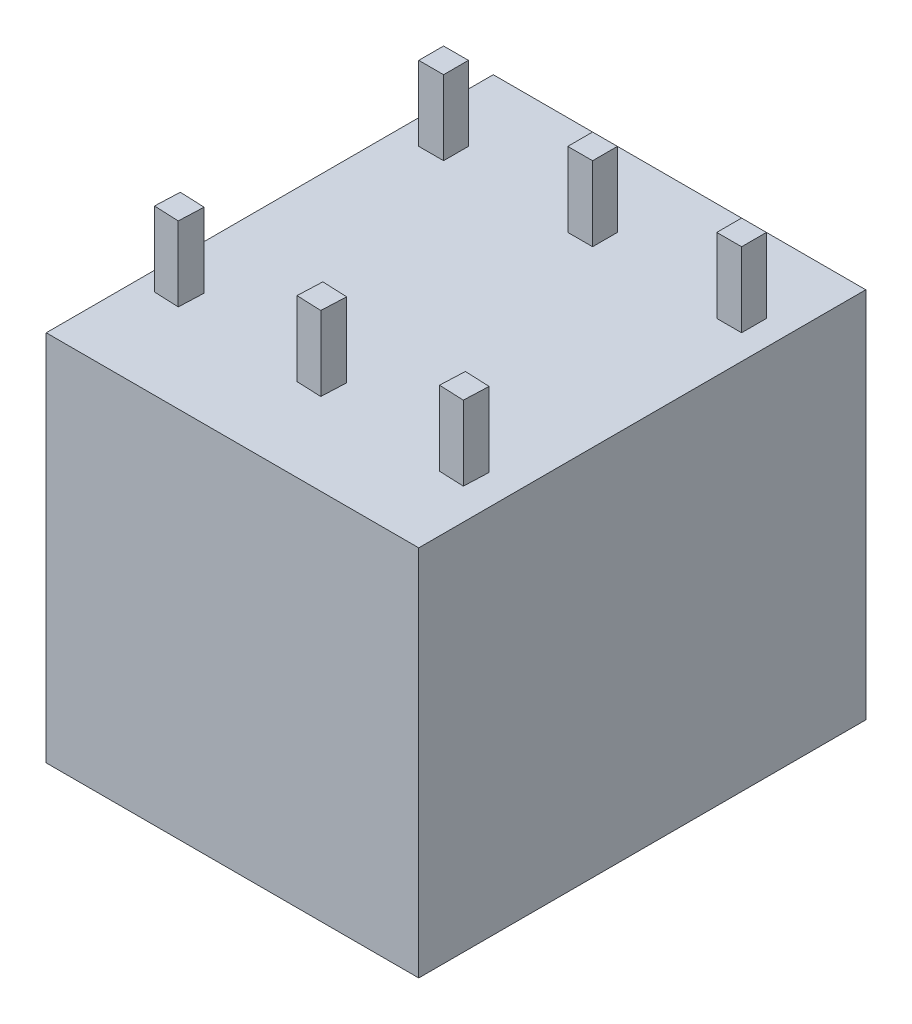
SolidWorks part; units mm, degrees
ref_plane "Plan de face" through (0, 0, 0) normal (0, 0, 1) x (1, 0, 0)
ref_plane "Plan de dessus" through (0, 0, 0) normal (0, 1, 0) x (1, 0, 0)
ref_plane "Plan de droite" through (0, 0, 0) normal (1, 0, 0) x (0, 0, -1)
sketch "Esquisse1" plane through (0, 0, 0) normal (0, 1, 0) x (1, 0, 0)
  line L1 (0, 0) -> (15, 0)
  line L2 (0, 0) -> (0, 18)
  line L3 (0, 18) -> (15, 18)
  line L4 (15, 0) -> (15, 18)
  dimension "D1" = 15
  dimension "D2" = 18
extrude "Boss.-Extru.1" add sketch "Esquisse1" along normal blind 15
sketch "Esquisse2" plane through (0, 15, 0) normal (0, 1, 0) x (1, 0, 0)
  line L0 (0, 18) -> (0, 0) construction
  line L1 (1, 15) -> (2, 15)
  line L2 (1, 15) -> (1, 14)
  line L3 (1, 14) -> (2, 14)
  line L4 (2, 15) -> (2, 14)
  line L5 (15, 18) -> (0, 18) construction
  line L6 (15, 18) -> (0, 18) construction
  line L7 (7, 15) -> (8, 15)
  line L8 (7, 15) -> (7, 14)
  line L9 (7, 14) -> (8, 14)
  line L10 (8, 15) -> (8, 14)
  line L11 (7.5, 18) -> (7.5, 0) construction
  line L12 (0, 0) -> (15, 0) construction
  line L13 (0, 9.3194) -> (15, 9) construction
  line L14 (15, 0) -> (15, 18) construction
  line L15 (14, 14) -> (13, 14)
  line L16 (14, 15) -> (14, 14)
  line L17 (14, 15) -> (13, 15)
  line L18 (13, 15) -> (13, 14)
  line L19 (12.7464, 3.0906) -> (12.789, 4.0897)
  line L20 (13.7455, 3.048) -> (12.7464, 3.0906)
  line L21 (13.7455, 3.048) -> (13.7881, 4.0471)
  line L22 (13.7881, 4.0471) -> (12.789, 4.0897)
  line L23 (7.7509, 3.3034) -> (7.7935, 4.3025)
  line L24 (6.7944, 4.3451) -> (7.7935, 4.3025)
  line L25 (6.7518, 3.346) -> (6.7944, 4.3451)
  line L26 (6.7518, 3.346) -> (7.7509, 3.3034)
  line L27 (1.7564, 3.5588) -> (1.7989, 4.5579)
  line L28 (0.7999, 4.6005) -> (1.7989, 4.5579)
  line L29 (0.7573, 3.6014) -> (0.7999, 4.6005)
  line L30 (0.7573, 3.6014) -> (1.7564, 3.5588)
  point P6 (1.5, 15)
  point P17 (7.5, 15)
  point P18 (7.5, 18)
  dimension "D1" = 1
  dimension "D2" = 1
  dimension "D3" = 1
  dimension "D4" = 3
  dimension "D5" = 1
  dimension "D6" = 1
  dimension "D7" = 3
extrude "Boss.-Extru.2" add sketch "Esquisse2" along normal blind 3
